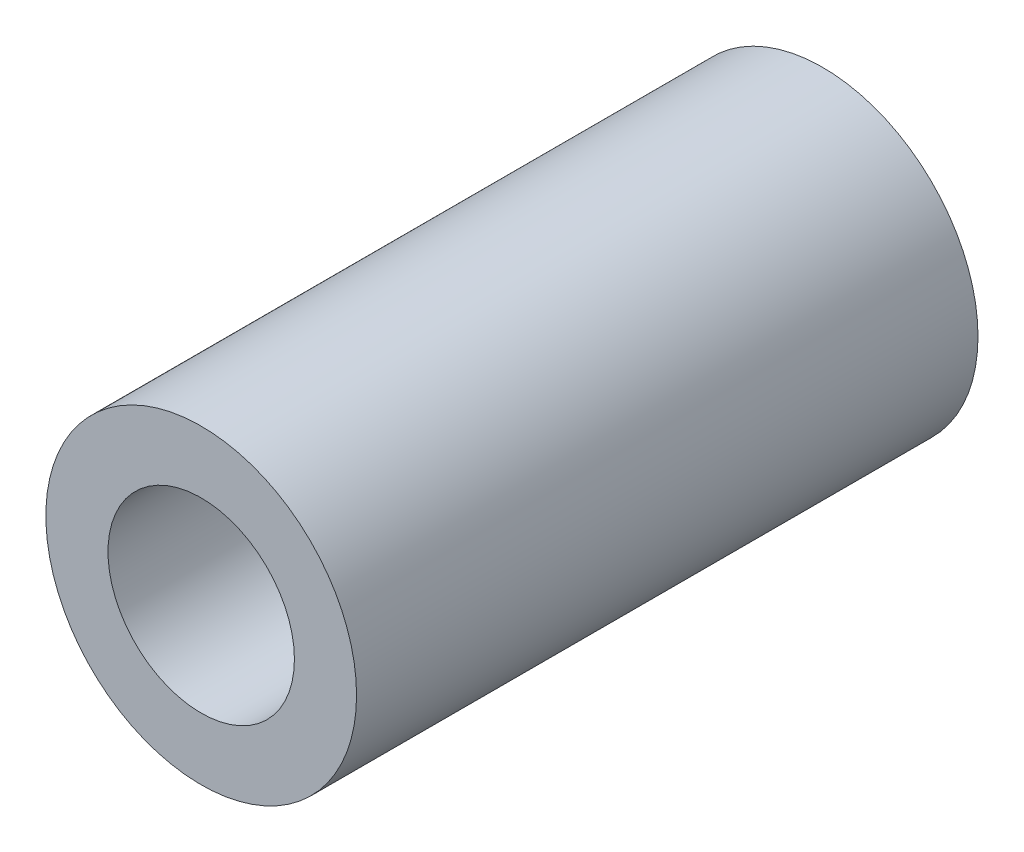
SolidWorks part; units mm, degrees
ref_plane "前视基准面" through (0, 0, 0) normal (0, 0, 1) x (1, 0, 0)
ref_plane "上视基准面" through (0, 0, 0) normal (0, 1, 0) x (1, 0, 0)
ref_plane "右视基准面" through (0, 0, 0) normal (1, 0, 0) x (0, 0, -1)
sketch "草图1" plane through (0, 0, 0) normal (0, 0, 1) x (1, 0, 0)
  circle A0 centre (0, 0) radius 2.5
  circle A1 centre (0, 0) radius 1.5
  dimension "D1" = 3
  dimension "D2" = 5
extrude "凸台-拉伸1" add sketch "草图1" along normal mid plane 10
